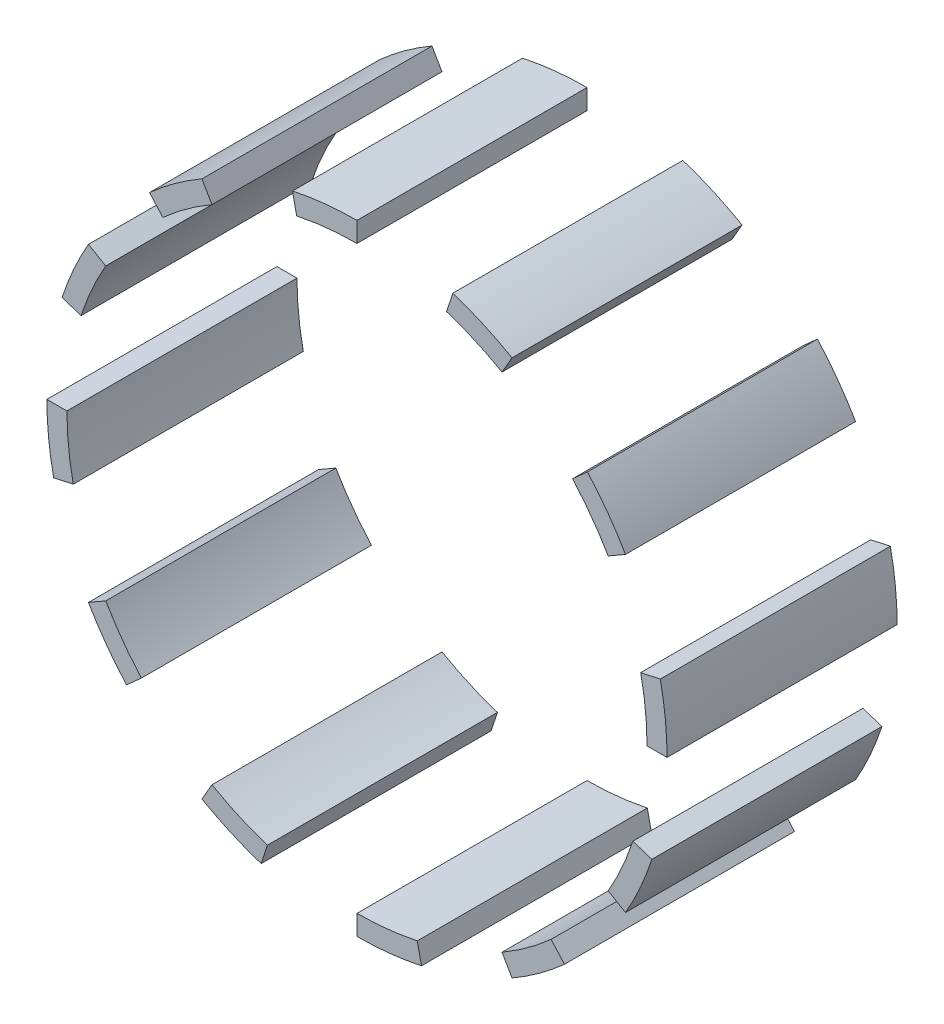
SolidWorks part; units mm, degrees
material "3.0255 (EN-AW 1350A)"
ref_plane "Plan de face" through (0, 0, 0) normal (0, 0, 1) x (1, 0, 0)
ref_plane "Plan de dessus" through (0, 0, 0) normal (0, 1, 0) x (1, 0, 0)
ref_plane "Plan de droite" through (0, 0, 0) normal (1, 0, 0) x (0, 0, -1)
sketch "Esquisse1" plane through (0, 0, 0) normal (0, 0, 1) x (1, 0, 0)
  line L0 (14.5, 0) -> (15.5, 0)
  line L1 (14.1831, 3.0147) -> (15.1613, 3.2226)
  line L2 (13.7903, -4.4807) -> (14.7414, -4.7898)
  line L3 (12.5574, -7.25) -> (13.4234, -7.75)
  line L4 (9.7024, -10.7756) -> (10.3715, -11.5187)
  line L5 (7.25, -12.5574) -> (7.75, -13.4234)
  line L6 (3.0147, -14.1831) -> (3.2226, -15.1613)
  line L7 (0, -14.5) -> (0, -15.5)
  line L8 (-4.4807, -13.7903) -> (-4.7898, -14.7414)
  line L9 (-7.25, -12.5574) -> (-7.75, -13.4234)
  line L10 (-10.7756, -9.7024) -> (-11.5187, -10.3715)
  line L11 (-12.5574, -7.25) -> (-13.4234, -7.75)
  line L12 (-14.1831, -3.0147) -> (-15.1613, -3.2226)
  line L13 (-14.5, 0) -> (-15.5, 0)
  line L14 (-13.7903, 4.4807) -> (-14.7414, 4.7898)
  line L15 (-12.5574, 7.25) -> (-13.4234, 7.75)
  line L16 (-9.7024, 10.7756) -> (-10.3715, 11.5187)
  line L17 (-7.25, 12.5574) -> (-7.75, 13.4234)
  line L18 (-3.0147, 14.1831) -> (-3.2226, 15.1613)
  line L19 (0, 14.5) -> (0, 15.5)
  line L20 (4.4807, 13.7903) -> (4.7898, 14.7414)
  line L21 (7.25, 12.5574) -> (7.75, 13.4234)
  line L22 (10.7756, 9.7024) -> (11.5187, 10.3715)
  line L23 (12.5574, 7.25) -> (13.4234, 7.75)
  arc A0 (14.5, 0) -> (14.1831, 3.0147) centre (0, 0) ccw
  arc A1 (15.5, 0) -> (15.1613, 3.2226) centre (0, 0) ccw
  arc A2 (12.5574, -7.25) -> (13.7903, -4.4807) centre (0, 0) ccw
  arc A3 (13.4234, -7.75) -> (14.7414, -4.7898) centre (0, 0) ccw
  arc A4 (7.25, -12.5574) -> (9.7024, -10.7756) centre (0, 0) ccw
  arc A5 (7.75, -13.4234) -> (10.3715, -11.5187) centre (0, 0) ccw
  arc A6 (0, -14.5) -> (3.0147, -14.1831) centre (0, 0) ccw
  arc A7 (0, -15.5) -> (3.2226, -15.1613) centre (0, 0) ccw
  arc A8 (-7.25, -12.5574) -> (-4.4807, -13.7903) centre (0, 0) ccw
  arc A9 (-7.75, -13.4234) -> (-4.7898, -14.7414) centre (0, 0) ccw
  arc A10 (-12.5574, -7.25) -> (-10.7756, -9.7024) centre (0, 0) ccw
  arc A11 (-13.4234, -7.75) -> (-11.5187, -10.3715) centre (0, 0) ccw
  arc A12 (-14.5, 0) -> (-14.1831, -3.0147) centre (0, 0) ccw
  arc A13 (-15.5, 0) -> (-15.1613, -3.2226) centre (0, 0) ccw
  arc A14 (-12.5574, 7.25) -> (-13.7903, 4.4807) centre (0, 0) ccw
  arc A15 (-13.4234, 7.75) -> (-14.7414, 4.7898) centre (0, 0) ccw
  arc A16 (-7.25, 12.5574) -> (-9.7024, 10.7756) centre (0, 0) ccw
  arc A17 (-7.75, 13.4234) -> (-10.3715, 11.5187) centre (0, 0) ccw
  arc A18 (0, 14.5) -> (-3.0147, 14.1831) centre (0, 0) ccw
  arc A19 (0, 15.5) -> (-3.2226, 15.1613) centre (0, 0) ccw
  arc A20 (7.25, 12.5574) -> (4.4807, 13.7903) centre (0, 0) ccw
  arc A21 (7.75, 13.4234) -> (4.7898, 14.7414) centre (0, 0) ccw
  arc A22 (12.5574, 7.25) -> (10.7756, 9.7024) centre (0, 0) ccw
  arc A23 (13.4234, 7.75) -> (11.5187, 10.3715) centre (0, 0) ccw
  point P53 (0, 0)
  dimension "D1" = 31
  dimension "D2" = 1
  dimension "D3" = 12
  dimension "D4" = 1
  dimension "D5" = 12
extrude "Boss.-Extru.1" add sketch "Esquisse1" along normal blind 11.5
